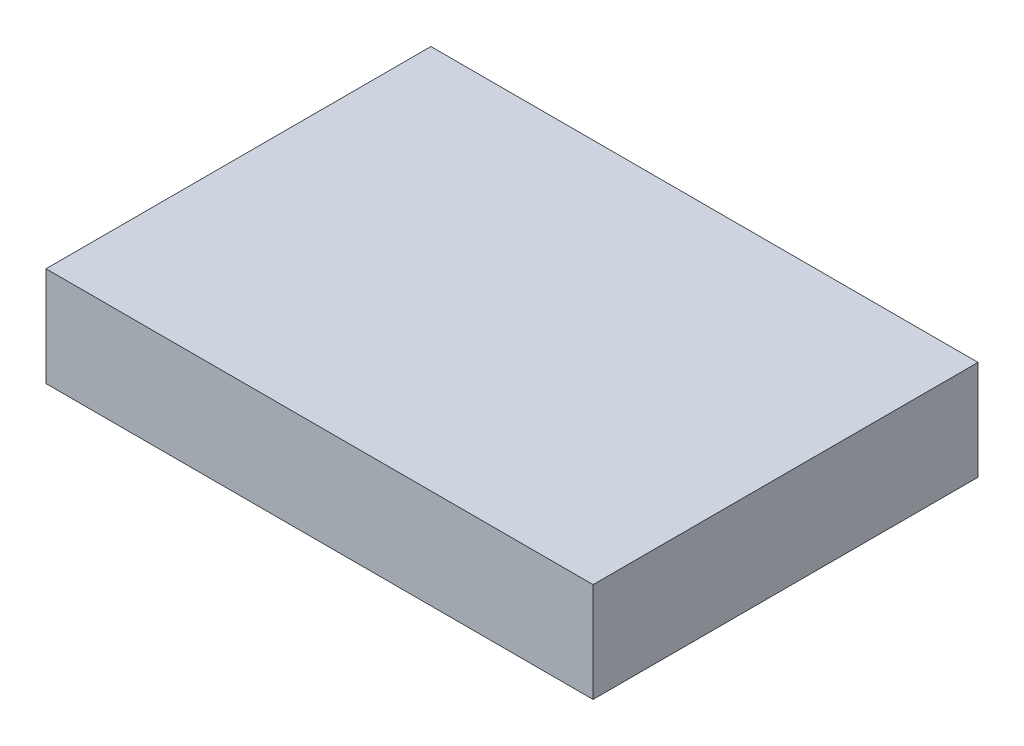
SolidWorks part; units mm, degrees
ref_plane "Front Plane" through (0, 0, 0) normal (0, 0, 1) x (1, 0, 0)
ref_plane "Top Plane" through (0, 0, 0) normal (0, 1, 0) x (1, 0, 0)
ref_plane "Right Plane" through (0, 0, 0) normal (1, 0, 0) x (0, 0, -1)
sketch "Sketch1" plane through (0, 0, 0) normal (0, 1, 0) x (1, 0, 0)
  line L1 (-12.65, -8.9) -> (12.65, -8.9)
  line L2 (-12.65, -8.9) -> (-12.65, 8.9)
  line L3 (-12.65, 8.9) -> (12.65, 8.9)
  line L4 (12.65, -8.9) -> (12.65, 8.9)
  line L5 (-12.65, -8.9) -> (12.65, 8.9) construction
  line L6 (-12.65, 8.9) -> (12.65, -8.9) construction
  point P0 (0, 0)
  dimension "D1" = 17.8
  dimension "D2" = 25.3
extrude "Boss-Extrude1" add sketch "Sketch1" along normal mid plane 4.6
